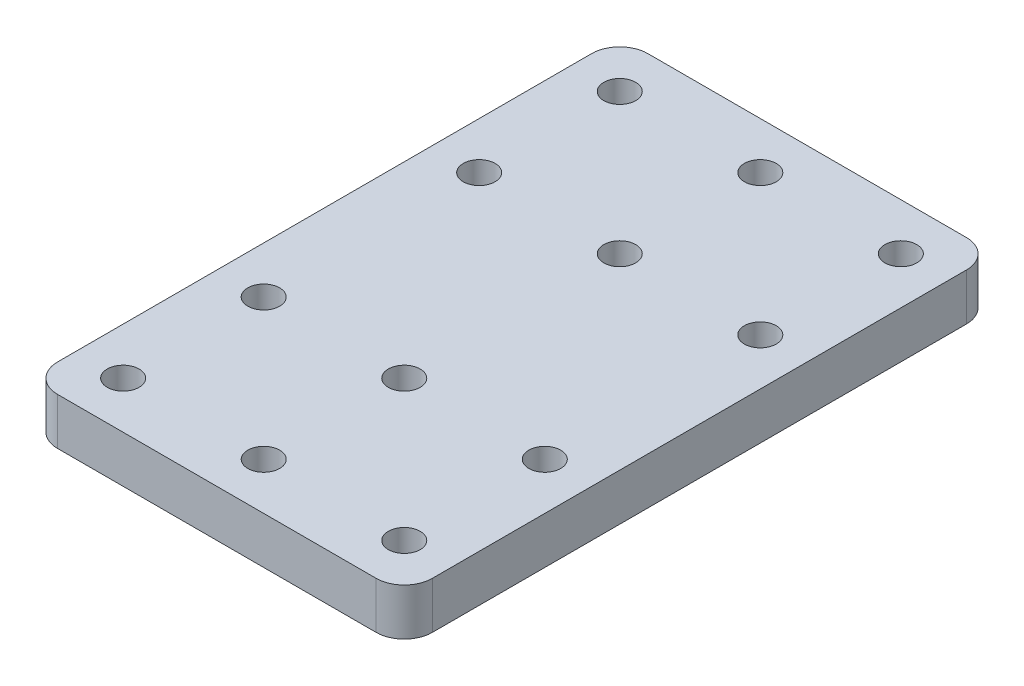
SolidWorks part; units mm, degrees
ref_plane "正面(Front)" through (0, 0, 0) normal (0, 0, 1) x (1, 0, 0)
ref_plane "平面(Top)" through (0, 0, 0) normal (0, 1, 0) x (1, 0, 0)
ref_plane "右側面(Right)" through (0, 0, 0) normal (1, 0, 0) x (0, 0, -1)
sketch "ｽｹｯﾁ1" plane through (0, 0, 0) normal (0, 1, 0) x (1, 0, 0)
  line L0 (-15, 11.5) -> (-15, -11.5) construction
  line L1 (-20, 31.5) -> (20, 31.5)
  line L2 (-20, 31.5) -> (-20, -31.5)
  line L3 (-20, -31.5) -> (20, -31.5)
  line L4 (20, 31.5) -> (20, -31.5)
  line L5 (-20, 31.5) -> (20, -31.5) construction
  line L6 (-20, -31.5) -> (20, 31.5) construction
  line L7 (-15, -11.5) -> (-15, -26.5) construction
  circle A0 centre (-15, 26.5) radius 1.7
  circle A1 centre (0, 26.5) radius 1.7
  circle A2 centre (15, 26.5) radius 1.7
  circle A3 centre (0, 11.5) radius 1.7
  circle A4 centre (-15, 11.5) radius 1.7
  circle A5 centre (15, 11.5) radius 1.7
  circle A6 centre (-15, -11.5) radius 1.7
  circle A7 centre (0, -11.5) radius 1.7
  circle A8 centre (15, -11.5) radius 1.7
  circle A9 centre (-15, -26.5) radius 1.7
  circle A10 centre (0, -26.5) radius 1.7
  circle A11 centre (15, -26.5) radius 1.7
  point P0 (0, 0)
  dimension "D1" = 5
  dimension "D2" = 3.4
  dimension "D3" = 15
  dimension "D4" = 15
  dimension "D5" = 5
  dimension "D6" = 5
  dimension "D13" = 5
  dimension "D8" = 15
  dimension "D10" = 23
  dimension "D12" = 15
  dimension "D7" = 2
  dimension "D9" = 2
  dimension "D11" = 2
extrude "ﾎﾞｽ - 押し出し1" add sketch "ｽｹｯﾁ1" along normal blind 5
fillet "ﾌｨﾚｯﾄ1" radius 3 4 edges at (20, 2.5, 31.5) (-20, 2.5, 31.5) (-20, 2.5, -31.5) (20, 2.5, -31.5)
